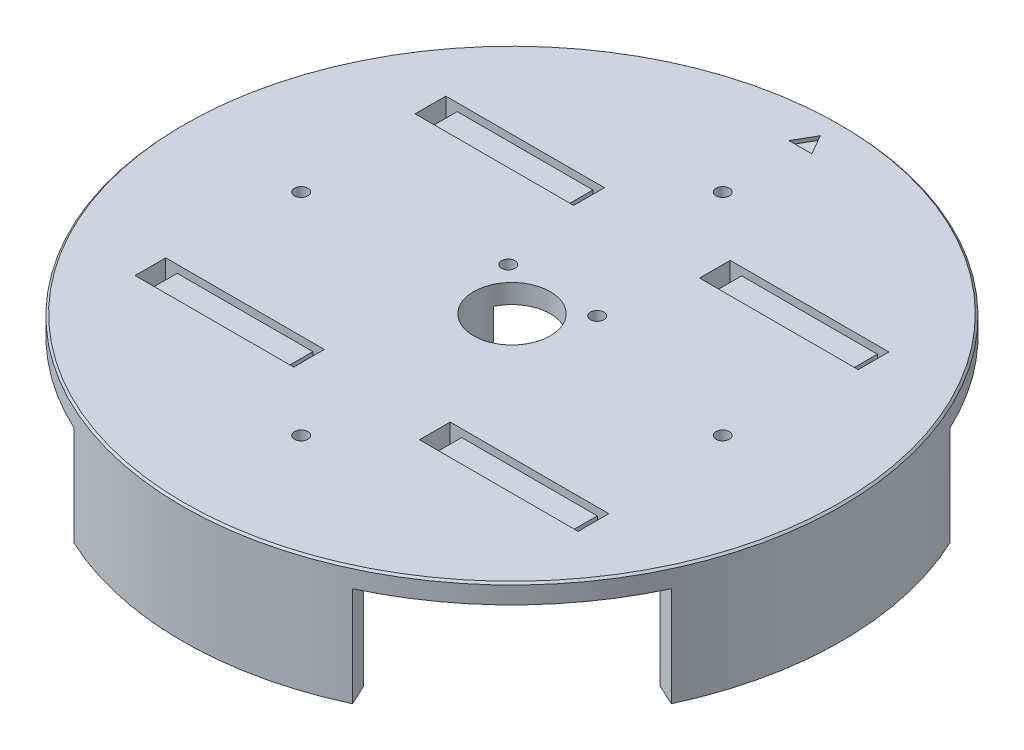
SolidWorks part; units mm, degrees
ref_plane "Ebene vorne" through (0, 0, 0) normal (0, 0, 1) x (1, 0, 0)
ref_plane "Ebene oben" through (0, 0, 0) normal (0, 1, 0) x (1, 0, 0)
ref_plane "Ebene rechts" through (0, 0, 0) normal (1, 0, 0) x (0, 0, -1)
sketch "Skizze1" plane through (0, 0, 0) normal (0, 1, 0) x (1, 0, 0)
  circle A0 centre (0, 0) radius 86
  dimension "D1" = 172
extrude "Aufsatz-Linear austragen1" add sketch "Skizze1" along normal blind 5
sketch "Skizze2" plane through (0, 0, 0) normal (0, -1, 0) x (1, 0, 0)
  line L0 (0, 0) -> (0, 86) construction
  line L1 (-36.3452, 77.9425) -> (-33.8095, 72.5046)
  line L2 (0, 0) -> (-36.3452, 77.9425) construction
  line L3 (36.3452, 77.9425) -> (33.8095, 72.5046)
  arc A2 (36.3452, 77.9425) -> (-36.3452, 77.9425) centre (0, 0) ccw
  arc A3 (33.8095, 72.5046) -> (-33.8095, 72.5046) centre (0, 0) ccw
  circle A9 centre (0, 0) radius 86 construction
  dimension "D2" = 6
  dimension "D1" = 25
extrude "Aufsatz-Linear austragen2" add sketch "Skizze2" along normal up to surface (26 mm away)
pattern_circular "Kreismuster1" count 4 over 360 about axis through (0, -99.9325, 0) along (0, 1, 0) of "Aufsatz-Linear austragen2"
sketch "Skizze4" plane through (0, 0, 0) normal (0, -1, 0) x (1, 0, 0)
  circle A0 centre (0, 0) radius 10
extrude "Schnitt-Linear austragen1" cut sketch "Skizze4" against normal up to next
sketch "Skizze7" plane through (0, 0, 0) normal (0, -1, 0) x (1, 0, 0)
  line L0 (-72.5046, 33.8095) -> (0, 0)
  line L1 (0, 0) -> (-72.5046, -33.8095)
  line L2 (0, 0) -> (72.5046, 33.8095)
  line L3 (0, 0) -> (72.5046, -33.8095)
  circle A0 centre (0, 0) radius 10 construction
  circle A1 centre (0, 0) radius 10
  circle A2 centre (0, 0) radius 13
  circle M1 centre (0, 0) radius 10
  dimension "D1" = 3
extrude "Aufsatz-Linear austragen5" add sketch "Skizze7" along normal up to surface (26 mm away) contours L0 A2 L1 M1 | L3 A2 L2 M1
sketch "Skizze6" plane through (0, -26, 0) normal (0, -1, 0) x (1, 0, 0)
  circle A0 centre (-21.4561, 80.0752) radius 1.35
  circle A2 centre (21.4561, 80.0752) radius 1.35
  dimension "D1" = 2.7
extrude "Schnitt-Linear austragen2" cut sketch "Skizze6" against normal blind 10
pattern_circular "Kreismuster2" count 4 over 360 about axis through (0, 0, 0) along (0, 1, 0) of "Schnitt-Linear austragen2"
fillet "Verrundung3" radius 3 6 edges at (0, 0, -80) (80, 0, 0) (0, 0, 80) (-80, 0, 0) (13, 0, 0) (-13, 0, 0)
sketch "Skizze10" plane through (0, 0, 0) normal (0, -1, 0) x (1, 0, 0)
  line L0 (-69.7857, 32.5416) -> (-69.7857, -32.5416) construction
  line L1 (-69.7857, 32.5416) -> (69.7857, 32.5416) construction
  line L2 (-69.7857, -32.5416) -> (69.7857, -32.5416) construction
  line L3 (69.7857, 32.5416) -> (69.7857, -32.5416) construction
  line L4 (57.8126, 32.5416) -> (54.8126, 32.5416)
  line L5 (57.8126, 32.5416) -> (57.8126, 40.5416)
  line L6 (54.8126, 32.5416) -> (54.8126, 40.5416)
  line L7 (57.8126, 40.5416) -> (54.8126, 40.5416)
  line L8 (-86, 0) -> (86, 0) construction
  line L9 (57.6126, -63.9727) -> (57.6126, 64.0273) construction
  line L10 (37.1126, 64.0273) -> (37.1126, -63.9727) construction
  line L11 (45.6126, 64.0273) -> (28.6126, 64.0273) construction
  line L12 (0, 86) -> (0, -86) construction
  line L13 (19.4126, 32.5416) -> (19.4126, 40.5416)
  line L14 (16.4126, 40.5416) -> (19.4126, 40.5416)
  line L15 (16.4126, 32.5416) -> (16.4126, 40.5416)
  line L16 (16.4126, 32.5416) -> (19.4126, 32.5416)
  line L17 (-19.4126, 32.5416) -> (-19.4126, 40.5416)
  line L18 (-16.4126, 40.5416) -> (-19.4126, 40.5416)
  line L19 (-16.4126, 32.5416) -> (-16.4126, 40.5416)
  line L20 (-16.4126, 32.5416) -> (-19.4126, 32.5416)
  line L21 (-57.8126, 40.5416) -> (-54.8126, 40.5416)
  line L22 (-57.8126, 32.5416) -> (-57.8126, 40.5416)
  line L23 (-57.8126, 32.5416) -> (-54.8126, 32.5416)
  line L24 (-54.8126, 32.5416) -> (-54.8126, 40.5416)
  line L25 (57.8126, -40.5416) -> (54.8126, -40.5416)
  line L26 (54.8126, -32.5416) -> (54.8126, -40.5416)
  line L27 (57.8126, -32.5416) -> (57.8126, -40.5416)
  line L28 (57.8126, -32.5416) -> (54.8126, -32.5416)
  line L29 (16.4126, -32.5416) -> (19.4126, -32.5416)
  line L30 (16.4126, -32.5416) -> (16.4126, -40.5416)
  line L31 (16.4126, -40.5416) -> (19.4126, -40.5416)
  line L32 (19.4126, -32.5416) -> (19.4126, -40.5416)
  line L33 (-16.4126, -32.5416) -> (-19.4126, -32.5416)
  line L34 (-16.4126, -32.5416) -> (-16.4126, -40.5416)
  line L35 (-16.4126, -40.5416) -> (-19.4126, -40.5416)
  line L36 (-19.4126, -32.5416) -> (-19.4126, -40.5416)
  line L37 (-54.8126, -32.5416) -> (-54.8126, -40.5416)
  line L38 (-57.8126, -32.5416) -> (-54.8126, -32.5416)
  line L39 (-57.8126, -32.5416) -> (-57.8126, -40.5416)
  line L40 (-57.8126, -40.5416) -> (-54.8126, -40.5416)
  arc A0 (-77.9425, 36.3452) -> (-77.9425, -36.3452) centre (0, 0) ccw construction
  arc A1 (77.9425, -36.3452) -> (77.9425, 36.3452) centre (0, 0) ccw construction
  arc A2 (36.3452, 77.9425) -> (-36.3452, 77.9425) centre (0, 0) ccw construction
  arc A3 (-36.3452, -77.9425) -> (36.3452, -77.9425) centre (0, 0) ccw construction
  dimension "D1" = 3
  dimension "D2" = 0.2
  dimension "D3" = 8
extrude "Schnitt-Linear austragen4" cut sketch "Skizze10" against normal up to next
chamfer "Fase1" distance 0.5 angle 45 1 edges at (0, 5, 86)
sketch "Skizze11" plane through (0, 5, 0) normal (0, 1, 0) x (1, 0, 0)
  line L0 (0, 80.4641) -> (0, 0) construction
  line L1 (3, 75.2679) -> (0, 80.4641)
  line L2 (0, 80.4641) -> (-3, 75.2679)
  line L3 (-3, 75.2679) -> (3, 75.2679)
  line L4 (0, 80.4641) -> (0, 85.5) construction
  circle A0 centre (0, 77) radius 1.7321 construction
  circle A1 centre (0, 0) radius 85.5 construction
  arc A3 (32.5416, 69.7857) -> (-32.5416, 69.7857) centre (0, 0) ccw construction
  dimension "D1" = 6
extrude "Schnitt-Linear austragen5" cut sketch "Skizze11" against normal blind 1
sketch "Skizze12" plane through (0, 0, 0) normal (0, -1, 0) x (1, 0, 0)
  circle A0 centre (-55, 0) radius 1.75
  circle A1 centre (0, -55) radius 1.75
  circle A2 centre (55, 0) radius 1.75
  circle A3 centre (0, 55) radius 1.75
  circle A4 centre (-11.6052, -10.6442) radius 1.75
  circle A5 centre (11.6052, -10.6442) radius 1.75
  dimension "D1" = 3.5
extrude "Schnitt-Linear austragen6" cut sketch "Skizze12" against normal blind 5
sketch "Skizze13" plane through (0, 5, 0) normal (0, 1, 0) x (1, 0, 0)
  line L1 (-54.8126, 40.5416) -> (-19.4126, 40.5416)
  line L2 (-54.8126, 40.5416) -> (-54.8126, 32.5416)
  line L3 (-54.8126, 32.5416) -> (-19.4126, 32.5416)
  line L4 (-19.4126, 40.5416) -> (-19.4126, 32.5416)
  line L5 (-54.8126, -32.5416) -> (-19.4126, -32.5416)
  line L6 (-54.8126, -32.5416) -> (-54.8126, -40.5416)
  line L7 (-54.8126, -40.5416) -> (-19.4126, -40.5416)
  line L8 (-19.4126, -32.5416) -> (-19.4126, -40.5416)
  line L9 (19.4126, -32.5416) -> (54.8126, -32.5416)
  line L10 (19.4126, -32.5416) -> (19.4126, -40.5416)
  line L11 (19.4126, -40.5416) -> (54.8126, -40.5416)
  line L12 (54.8126, -32.5416) -> (54.8126, -40.5416)
  line L13 (19.4126, 40.5416) -> (54.8126, 40.5416)
  line L14 (19.4126, 40.5416) -> (19.4126, 32.5416)
  line L15 (19.4126, 32.5416) -> (54.8126, 32.5416)
  line L16 (54.8126, 40.5416) -> (54.8126, 32.5416)
extrude "Schnitt-Linear austragen7" cut sketch "Skizze13" against normal blind 2
